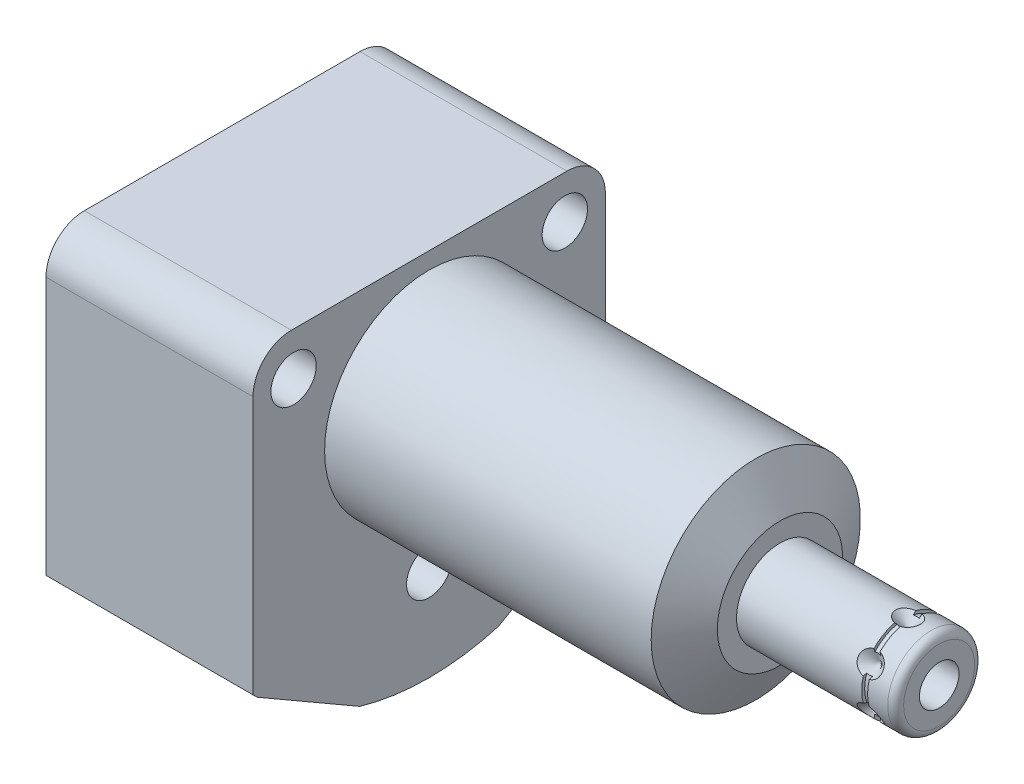
SolidWorks part; units mm, degrees
material "Alloy Steel"
ref_plane "Front Plane" through (0, 0, 0) normal (0, 0, 1) x (1, 0, 0)
ref_plane "Top Plane" through (0, 0, 0) normal (0, 1, 0) x (1, 0, 0)
ref_plane "Right Plane" through (0, 0, 0) normal (1, 0, 0) x (0, 0, -1)
sketch "Sketch1" plane through (0, 0, 0) normal (1, 0, 0) x (0, 0, -1)
  line L0 (-22.5044, 15.494) -> (-22.5044, -22.3968)
  line L1 (-21.968, -22.9231) -> (-8.868, -30.4864)
  line L2 (8.868, -30.4864) -> (21.968, -22.9231)
  line L3 (22.5044, -22.3968) -> (22.5044, 15.494)
  line L4 (22.5044, 15.494) -> (-22.5044, 15.494)
  line L5 (0, -34.1122) -> (0, 17.8562) construction
  line L6 (-36.4519, 0) -> (54.4719, 0) construction
  arc A0 (-8.868, -30.4864) -> (8.868, -30.4864) centre (0, 0) ccw
  arc A1 (-22.5044, -22.3968) -> (-21.968, -22.9231) centre (0, 0) ccw
  arc A2 (21.968, -22.9231) -> (22.5044, -22.3968) centre (0, 0) ccw
  dimension "D6" = 31.75
  dimension "D1" = 45.0088
  dimension "D2" = 30.836
  dimension "D3" = 45.0088
  dimension "D4" = 15.494
  dimension "D5" = 30
extrude "Extrude1" add sketch "Sketch1" along normal blind 44.8056 and the other way blind 26.4414
sketch "Sketch2" plane through (0, 0, 0) normal (1, 0, 0) x (0, 0, -1)
  line L6 (22.5044, 15.494) -> (-22.5044, 15.494)
  line L7 (-22.5044, 15.494) -> (-22.5044, -22.3968)
  line L8 (-21.968, -22.9231) -> (-8.868, -30.4864)
  line L9 (8.868, -30.4864) -> (21.968, -22.9231)
  line L10 (22.5044, -22.3968) -> (22.5044, 15.494)
  line L11 (22.5044, 15.494) -> (-22.5044, 15.494)
  line L12 (-22.5044, 15.494) -> (-22.5044, -22.3968)
  line L13 (-21.968, -22.9231) -> (-8.868, -30.4864)
  line L14 (8.868, -30.4864) -> (21.968, -22.9231)
  line L15 (22.5044, -22.3968) -> (22.5044, 15.494)
  circle A0 centre (0, 0) radius 13.3604
  arc A4 (-22.5044, -22.3968) -> (-21.968, -22.9231) centre (0, 0) ccw
  arc A5 (-8.868, -30.4864) -> (8.868, -30.4864) centre (0, 0) ccw
  arc A6 (21.968, -22.9231) -> (22.5044, -22.3968) centre (0, 0) ccw
  arc A7 (-22.5044, -22.3968) -> (-21.968, -22.9231) centre (0, 0) ccw
  arc A8 (-8.868, -30.4864) -> (8.868, -30.4864) centre (0, 0) ccw
  arc A9 (21.968, -22.9231) -> (22.5044, -22.3968) centre (0, 0) ccw
  dimension "D2" = 26.7208
  dimension "D1" = 0
extrude "Cut-Extrude1" cut sketch "Sketch2" along normal up to next
sketch "Sketch3" plane through (0, 0, 0) normal (0, 0, 1) x (1, 0, 0)
  line L0 (41.7113, 13.3604) -> (44.8056, 8.001)
  line L1 (23.3045, 0) -> (44.9603, 0) construction
  line L2 (44.8056, 13.3604) -> (44.8056, 8.001)
  line L3 (44.8056, 13.3604) -> (41.7113, 13.3604)
  line L4 (44.8056, -13.3604) -> (44.8056, 13.3604) construction
  line L5 (44.8056, 13.3604) -> (0, 13.3604) construction
  dimension "D1" = 30
  dimension "D2" = 16.002
revolve "Cut-Revolve1" cut sketch "Sketch3" angle 360 about L1
ref_plane "Plane19" through (0, 0, 10.49) normal (0, 0, 1) x (1, 0, 0)
sketch "S2D0002" plane through (-24.9936, -18.1864, 10.49) normal (0, 0, 1) x (0, 1, 0)
  line L0 (3.2512, 0) -> (5.7023, 0)
  line L1 (3.2512, 0) -> (3.2512, -2.9972)
  line L2 (3.2512, -2.9972) -> (1.2446, -2.9972)
  line L3 (1.2446, -2.9972) -> (1.2446, -11.9888)
  line L4 (1.2446, -11.9888) -> (0, -11.9888)
  line L5 (0, -11.9888) -> (0, 1.4478)
  line L6 (0, -23.5585) -> (0, 0.5994) construction
  line L7 (5.7023, 0) -> (5.7023, 1.4478)
  line L8 (33.6804, 1.4478) -> (-4.2104, 1.4478) construction
  line L9 (5.7023, 1.4478) -> (0, 1.4478)
  dimension "D1" = 1.4478
  dimension "D2" = 18.1864
  dimension "D3" = 11.4046
  dimension "D4" = 6.5024
  dimension "D5" = 2.4892
  dimension "D6" = 8.9916
  dimension "D7" = 2.9972
revolve "Cut-Revolve2" cut sketch "S2D0002" angle 360 about L6
ref_plane "Plane20" through (-12.9286, 0, 0) normal (1, 0, 0) x (0, 0, -1)
sketch "Sketch6" plane through (-12.9286, 0, 0) normal (1, 0, 0) x (0, 0, -1)
  line L0 (-19.5804, -24.0083) -> (-22.4357, -22.3598)
  line L1 (-19.5804, -24.0083) -> (-19.5169, -23.8983)
  line L2 (-19.5169, -23.8983) -> (-18.7883, -23.7031)
  line L3 (-18.7883, -23.7031) -> (-13.8353, -15.1242)
  line L4 (-13.8353, -15.1242) -> (-10.0078, -17.334)
  line L5 (-10.0078, -17.334) -> (-15.418, -26.7048)
  line L6 (-6.5499, -11.3447) -> (3.1494, 5.455) construction
  line L7 (-22.4357, -22.3598) -> (-22.5627, -22.5798)
  line L8 (-21.968, -22.9231) -> (-8.868, -30.4864) construction
  line L9 (-22.5627, -22.5798) -> (-15.418, -26.7048)
  line L10 (-21.968, -22.9231) -> (-8.868, -30.4864) construction
  dimension "D1" = 0.254
  dimension "D2" = 16.5
  dimension "D3" = 45
  dimension "D4" = 0.6604
  dimension "D5" = 9.906
  dimension "D6" = 8.8392
  dimension "D7" = 10.5664
  dimension "D8" = 0.127
revolve "Cut-Revolve4" cut sketch "Sketch6" angle 360 about L6
mirror "Mirror1" about plane through (0, 0, 0) normal (0, 0, 1) of "Cut-Revolve2", "Cut-Revolve4"
sketch "Sketch7" plane through (0, 0, 0) normal (0, 0, 1) x (1, 0, 0)
  line L0 (44.8056, 0) -> (44.8056, 5.5563)
  line L1 (44.8056, 5.5563) -> (64.1226, 5.5563)
  line L2 (65.1386, 4.5403) -> (65.1386, 0)
  line L3 (65.1386, 0) -> (44.8056, 0)
  line L4 (4.9931, 0) -> (66.1154, 0) construction
  line L5 (44.8056, -8.001) -> (44.8056, 8.001) construction
  line L6 (-26.4414, 15.494) -> (-26.4414, -22.3968) construction
  arc A0 (65.1386, 4.5403) -> (64.1226, 5.5563) centre (64.1226, 4.5403) ccw
  point P0 (44.8056, 0)
  dimension "D3" = 1.016
  dimension "D1" = 91.58
  dimension "D2" = 11.1125
revolve "Revolve1" add sketch "Sketch7" angle 360 about L4
sketch "S2D0001" plane through (0, 0, 0) normal (0, 0, 1) x (1, 0, 0)
  line L0 (65.1386, -2.5273) -> (54.9786, -2.5273)
  line L1 (54.9786, -2.5273) -> (53.46, 0)
  line L2 (65.1386, -2.5273) -> (65.1386, 0)
  line L3 (65.1386, 0) -> (53.46, 0)
  line L4 (-2.5273, 0) -> (-28.8062, 0) construction
  line L5 (65.1386, -4.5403) -> (65.1386, 4.5403) construction
  dimension "D1" = 5.0546
  dimension "D2" = 10.16
  dimension "D3" = 59
revolve "Cut-Revolve8" cut sketch "S2D0001" angle 360 about L4
sketch "Sketch9" plane through (0, 0, 0) normal (0, 0, 1) x (1, 0, 0)
  line L0 (61.1762, -5.5563) -> (59.5887, -5.5563)
  line L1 (59.5887, -5.5563) -> (61.1762, -3.9688)
  line L2 (61.1762, -5.5563) -> (61.1762, -3.9688)
  line L3 (61.1762, -6.2534) -> (61.1762, 0.0794) construction
  line L4 (44.8056, -5.5563) -> (64.1226, -5.5563) construction
  line L5 (65.1386, -4.5403) -> (65.1386, 4.5403) construction
  dimension "D1" = 3.9624
  dimension "D2" = 45
  dimension "D3" = 3.175
revolve "Cut-Revolve9" cut sketch "Sketch9" angle 360 about L3
sketch "Sketch11" plane through (0, 0, 0) normal (0, 1, 0) x (1, 0, 0)
  line L0 (61.5572, -5.5563) -> (61.5572, -5.1753)
  line L1 (61.5572, -5.1753) -> (60.7952, -5.1753)
  line L2 (60.7952, -5.1753) -> (60.7952, -5.5563)
  line L3 (60.7952, -5.5563) -> (61.5572, -5.5563)
  line L4 (0, 0) -> (83.4312, 0) construction
  line L6 (44.8056, -5.5563) -> (64.1226, -5.5563) construction
  line L7 (61.1762, 0) -> (61.1762, -20.2865) construction
  dimension "D1" = 0.762
  dimension "D2" = 0.381
revolve "Cut-Revolve5" cut sketch "Sketch11" angle 360 about L4
sketch "Sketch15" plane through (-21.9964, 0, 0) normal (-1, 0, 0) x (0, 0, 1)
  circle A0 centre (10.49, -18.1864) radius 2.7432
  circle A1 centre (10.49, -18.1864) radius 3.2512 construction
  dimension "D1" = 5.4864
extrude "Extrude3" add sketch "Sketch15" along normal blind 2.9972
sketch "Sketch16" plane through (-24.9936, 0, 0) normal (-1, 0, 0) x (0, 0, 1)
  line L7 (11.9271, -18.1864) -> (11.2086, -16.9418)
  line L8 (11.2086, -16.9418) -> (9.7714, -16.9418)
  line L9 (9.7714, -16.9418) -> (9.0529, -18.1864)
  line L10 (9.0529, -18.1864) -> (9.7714, -19.431)
  line L11 (9.7714, -19.431) -> (11.2086, -19.431)
  line L12 (11.2086, -19.431) -> (11.9271, -18.1864)
  circle A0 centre (10.49, -18.1864) radius 1.2446 construction
  dimension "D1" = 2.4892
extrude "Cut-Extrude2" cut sketch "Sketch16" against normal blind 2.54
chamfer "Chamfer1" distance 0.381 angle 45 1 edges at (-24.9936, -18.1864, 13.2332)
mirror "Mirror2" about plane through (0, 0, 0) normal (0, 0, 1) of "Extrude3", "Cut-Extrude2", "Chamfer1"
sketch "Sketch21" plane through (0, 0, 10.49) normal (0, 0, 1) x (1, 0, 0)
  line L0 (-35.9744, -18.1864) -> (-17.6399, -18.1864) construction
  line L1 (-13.0048, -16.9418) -> (-21.9964, -16.9418) construction
  line L2 (-21.9964, -19.431) -> (-17.3029, -19.431) construction
  line L3 (-24.9936, -12.4841) -> (-24.9936, -23.8887) construction
  circle A0 centre (-25.8572, -13.3731) radius 0.889
  dimension "D1" = 1.778
  dimension "D2" = 9.6266
  dimension "D3" = 0.8636
revolve "Revolve4" add sketch "Sketch21" angle 360 about L0
mirror "Mirror3" about plane through (0, 0, 0) normal (0, 0, 1) of bodies 129
fillet "Fillet1" radius 4.9022 2 edges at (-13.2207, 15.494, 22.5044) (-13.2207, 15.494, -22.5044)
hole_wizard "Hole1" positions "Sketch23" profile "Sketch22" legacy end condition up to next
sketch "Sketch23" plane through (0, 0, 0) normal (1, 0, 0) x (0, 0, -1)
  line L0 (0, 0) -> (0, 19.8912) construction
  point P0 (0, -19.9898)
  point P5 (-17.3228, 10.0076)
  point P13 (17.3228, 10.0076)
  dimension "D1" = 19.9898
  dimension "D2" = 10.0076
  dimension "D3" = 17.3228
sketch "Sketch22" plane through (0, -19.9898, 0) normal (0, 1, 0) x (0, 0, -1)
  line L0 (0, 0) -> (0, 26.4414)
  line L1 (0, 26.4414) -> (2.8955, 26.4414)
  line L2 (2.8955, 26.4414) -> (2.8955, 0)
  line L3 (2.8955, 0) -> (0, 0)
  line L4 (0, 110) -> (0, -10) construction
  dimension "Diameter" = 5.791
  dimension "Depth" = 26.4414
pattern_circular "CirPattern1" count 6 over 360 about axis through (0, 0, 0) along (1, 0, 0) of "Cut-Revolve9"
